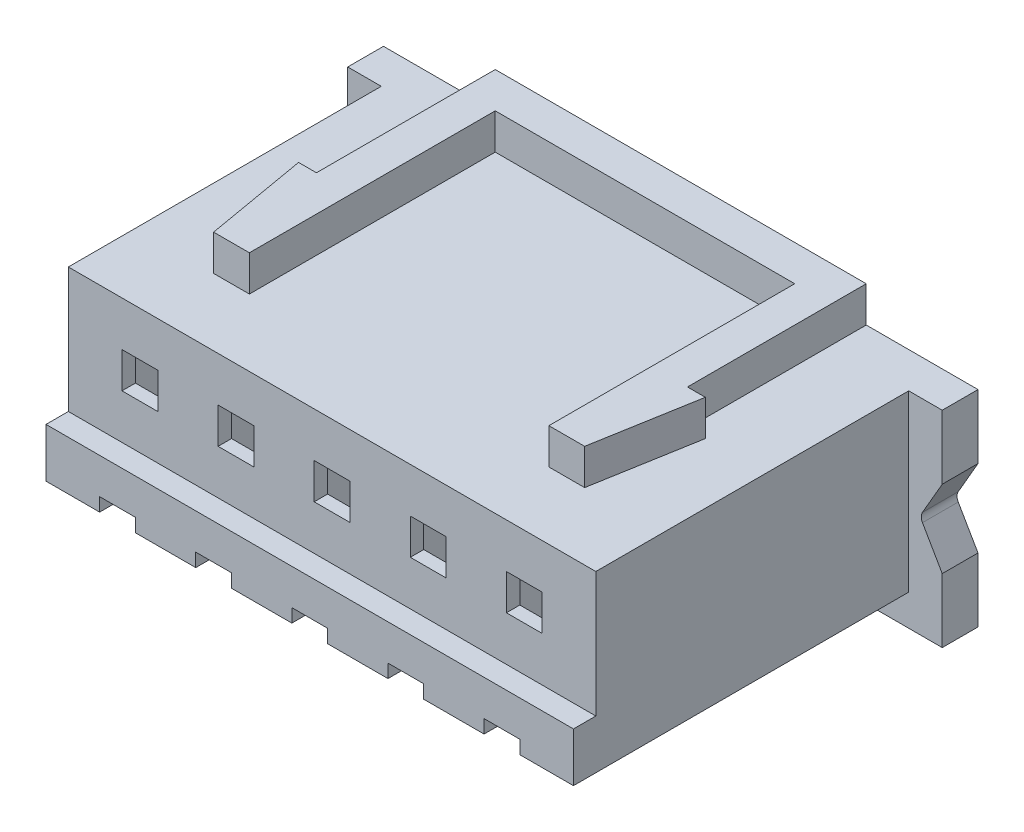
SolidWorks part; units mm, degrees
ref_plane "Front Plane" through (0, 0, 0) normal (0, 0, 1) x (1, 0, 0)
ref_plane "Top Plane" through (0, 0, 0) normal (0, 1, 0) x (1, 0, 0)
ref_plane "Right Plane" through (0, 0, 0) normal (1, 0, 0) x (0, 0, -1)
sketch "Sketch1" plane through (0, 0, 0) normal (0, 0, 1) x (1, 0, 0)
  line L1 (-5.9, -2.15) -> (5.9, -2.15)
  line L2 (-5.9, -2.15) -> (-5.9, 2.15)
  line L3 (-5.9, 2.15) -> (5.9, 2.15)
  line L4 (5.9, -2.15) -> (5.9, 2.15)
  line L5 (-5.9, -2.15) -> (5.9, 2.15) construction
  line L6 (-5.9, 2.15) -> (5.9, -2.15) construction
  point P0 (0, 0)
  dimension "D1" = 4.3
  dimension "D2" = 11.8
extrude "Boss-Extrude1" add sketch "Sketch1" along normal blind 7
sketch "Sketch2" plane through (0, 0, 0) normal (0, 0, -1) x (-1, 0, 0)
  line L0 (0, 0) -> (0, 2.15) construction
  line L1 (-6.65, 2.15) -> (6.65, 2.15)
  line L2 (-6.65, 2.15) -> (-6.65, -2.45)
  line L3 (-6.65, -2.45) -> (6.65, -2.45)
  line L4 (6.65, 2.15) -> (6.65, -2.45)
  dimension "D1" = 13.3
  dimension "D2" = 4.6
extrude "Boss-Extrude2" add sketch "Sketch2" along normal blind 0.8
sketch "Sketch3" plane through (0, 0, 0) normal (0, 0, 1) x (1, 0, 0)
  line L1 (6.65, 2.15) -> (6.65, -2.45) construction
  line L2 (6.15, -0.15) -> (6.65, -1.016)
  line L3 (6.15, -0.15) -> (6.65, 0.716)
  line L4 (6.65, -0.15) -> (6.15, -0.15) construction
  line L5 (6.65, 0.716) -> (6.65, -1.016)
  dimension "D1" = 60
  dimension "D2" = 0.5
  dimension "D3" = 60
extrude "Cut-Extrude1" cut sketch "Sketch3" against normal blind 1
fillet "Fillet1" radius 0.2 1 edges at (6.15, -0.15, -0.4)
sketch "Sketch4" plane through (0, 0, 7) normal (0, 0, 1) x (1, 0, 0)
  line L0 (-5.9, 2.15) -> (-5.9, -2.15) construction
  line L1 (-5.9, -0.65) -> (5.9, -0.65)
  line L2 (-5.9, -0.65) -> (-5.9, -2.15)
  line L3 (-5.9, -2.15) -> (5.9, -2.15)
  line L4 (5.9, -0.65) -> (5.9, -2.15)
  dimension "D1" = 1.5
extrude "Boss-Extrude3" add sketch "Sketch4" along normal blind 0.5
sketch "Sketch5" plane through (0, 0, 7.5) normal (0, 0, 1) x (1, 0, 0)
  line L0 (-5.9, -2.15) -> (5.9, -2.15) construction
  line L1 (-4.7, -1.45) -> (-3.9, -1.45)
  line L2 (-4.7, -1.45) -> (-4.7, -2.15)
  line L3 (-4.7, -2.15) -> (-3.9, -2.15)
  line L4 (-3.9, -1.45) -> (-3.9, -2.15)
  line L5 (-5.9, -0.65) -> (-5.9, -2.15) construction
  line L14 (3.9, -1.45) -> (4.7, -1.45)
  line L15 (4.7, -1.45) -> (4.7, -2.15)
  line L16 (3.9, -1.45) -> (3.9, -2.15)
  line L17 (3.9, -2.15) -> (4.7, -2.15)
  line L18 (5.9, -2.15) -> (5.9, -0.65) construction
  line L20 (1.75, -2.15) -> (2.55, -2.15)
  line L21 (1.75, -1.45) -> (1.75, -2.15)
  line L22 (1.75, -1.45) -> (2.55, -1.45)
  line L23 (2.55, -1.45) -> (2.55, -2.15)
  line L24 (-0.4, -2.15) -> (0.4, -2.15)
  line L25 (-0.4, -1.45) -> (-0.4, -2.15)
  line L26 (-0.4, -1.45) -> (0.4, -1.45)
  line L27 (0.4, -1.45) -> (0.4, -2.15)
  line L28 (-2.55, -2.15) -> (-1.75, -2.15)
  line L29 (-2.55, -1.45) -> (-2.55, -2.15)
  line L30 (-2.55, -1.45) -> (-1.75, -1.45)
  line L31 (-1.75, -1.45) -> (-1.75, -2.15)
  line L32 (-4.7, -2.15) -> (-3.9, -2.15)
  line L33 (-4.7, -1.45) -> (-4.7, -2.15)
  line L34 (-4.7, -1.45) -> (-3.9, -1.45)
  line L35 (-3.9, -1.45) -> (-3.9, -2.15)
  line L36 (-5.9, 2.15) -> (-5.9, -2.15) construction
  line L37 (1.0333, -1.45) -> (1.0333, -2.15) [skipped]
  line L38 (1.0333, -2.15) -> (1.8333, -2.15) [skipped]
  line L39 (1.8333, -1.45) -> (1.8333, -2.15) [skipped]
  line L40 (1.0333, -1.45) -> (1.8333, -1.45) [skipped]
  line L41 (-1.0333, -1.45) -> (-1.0333, -2.15) [skipped]
  line L42 (-1.8333, -2.15) -> (-1.0333, -2.15) [skipped]
  line L43 (-1.8333, -1.45) -> (-1.0333, -1.45) [skipped]
  line L44 (-1.8333, -1.45) -> (-1.8333, -2.15) [skipped]
  line M18 (-5.9, -2.15) -> (5.9, -2.15)
  dimension "D1" = 0.8
  dimension "D2" = 1.2
  dimension "D3" = 0.7
  dimension "D5" = 1.2
  dimension "D8" = 1.2
  dimension "D4" = 4
  dimension "D7" = 5
extrude "Cut-Extrude2" cut sketch "Sketch5" against normal blind 3.2 contours L14 L16 L15 M18 | L23 L22 L21 M18 | L27 L26 L25 M18 | L31 L30 L29 M18 | L4 L1 L2 M18
sketch "Sketch6" plane through (0, 0, 7) normal (0, 0, 1) x (1, 0, 0)
  line L0 (-5.9, 2.15) -> (-5.9, -0.65) construction
  line L1 (-4.7, 1.15) -> (-3.9, 1.15)
  line L2 (-4.7, 1.15) -> (-4.7, 0.35)
  line L3 (-4.7, 0.35) -> (-3.9, 0.35)
  line L4 (-3.9, 1.15) -> (-3.9, 0.35)
  line L5 (-1.75, 1.15) -> (-1.75, 0.35)
  line L6 (-2.55, 0.35) -> (-1.75, 0.35)
  line L7 (-2.55, 1.15) -> (-2.55, 0.35)
  line L8 (-2.55, 1.15) -> (-1.75, 1.15)
  line L9 (0.4, 1.15) -> (0.4, 0.35)
  line L10 (-0.4, 0.35) -> (0.4, 0.35)
  line L11 (-0.4, 1.15) -> (-0.4, 0.35)
  line L12 (-0.4, 1.15) -> (0.4, 1.15)
  line L13 (2.55, 1.15) -> (2.55, 0.35)
  line L14 (1.75, 0.35) -> (2.55, 0.35)
  line L15 (1.75, 1.15) -> (1.75, 0.35)
  line L16 (1.75, 1.15) -> (2.55, 1.15)
  line L18 (5.9, 2.15) -> (-5.9, 2.15) construction
  line L19 (4.7, 1.15) -> (4.7, 0.35)
  line L20 (3.9, 0.35) -> (4.7, 0.35)
  line L21 (3.9, 1.15) -> (3.9, 0.35)
  line L22 (3.9, 1.15) -> (4.7, 1.15)
  line L23 (5.9, -0.65) -> (5.9, 2.15) construction
  dimension "D1" = 0.8
  dimension "D2" = 0.8
  dimension "D3" = 1.2
  dimension "D5" = 1.2
  dimension "D6" = 1
  dimension "D4" = 5
extrude "Cut-Extrude3" cut sketch "Sketch6" against normal blind 10
sketch "Sketch7" plane through (0, 2.15, 0) normal (0, 1, 0) x (1, 0, 0)
  line L0 (-4.15, -5.5) -> (-4.55, -3.2)
  line L1 (-4.55, -3.2) -> (-4.15, -3.2)
  line L2 (-4.15, -3.2) -> (-4.15, 0.8)
  line L3 (-6.65, 0.8) -> (6.65, 0.8) construction
  line L4 (-4.15, 0.8) -> (4.15, 0.8)
  line L5 (4.15, 0.8) -> (4.15, -3.2)
  line L6 (4.15, -3.2) -> (4.55, -3.2)
  line L7 (4.55, -3.2) -> (4.15, -5.5)
  line L8 (4.15, -5.5) -> (3.35, -5.5)
  line L9 (3.35, -5.5) -> (3.35, 0)
  line L10 (3.35, 0) -> (-3.35, 0)
  line L11 (-3.35, 0) -> (-3.35, -5.5)
  line L12 (-3.35, -5.5) -> (-4.15, -5.5)
  line L13 (0, 0.8) -> (0, 0) construction
  dimension "D1" = 0.8
  dimension "D2" = 0.8
  dimension "D3" = 0.8
  dimension "D4" = 0.8
  dimension "D5" = 1.2
  dimension "D6" = 4
  dimension "D7" = 2.3
  dimension "D8" = 4
  dimension "D9" = 1.2
  dimension "D10" = 0.8
  dimension "D11" = 8.3
extrude "Boss-Extrude4" add sketch "Sketch7" along normal blind 0.8
sketch "Sketch8" plane through (0, 0, -0.8) normal (0, 0, -1) x (-1, 0, 0)
  line L1 (5.3, 1.75) -> (3.3, 1.75)
  line L2 (5.3, 1.75) -> (5.3, -1.05)
  line L3 (4.7, -1.05) -> (4.7, -1.45)
  line L4 (3.3, 1.75) -> (3.3, -1.05)
  line L5 (5.3, -1.05) -> (4.7, -1.05)
  line L6 (4.7, -1.45) -> (3.9, -1.45)
  line L7 (3.9, -1.45) -> (3.9, -1.05)
  line L8 (3.9, -1.05) -> (3.3, -1.05)
  line L11 (3.15, -1.05) -> (2.55, -1.05)
  line L12 (2.55, -1.05) -> (2.55, -1.45)
  line L13 (2.55, -1.45) -> (1.75, -1.45)
  line L14 (1.75, -1.05) -> (1.15, -1.05)
  line L15 (1.75, -1.45) -> (1.75, -1.05)
  line L16 (1.15, 1.75) -> (1.15, -1.05)
  line L17 (3.15, 1.75) -> (1.15, 1.75)
  line L18 (3.15, 1.75) -> (3.15, -1.05)
  line L19 (1, -1.05) -> (0.4, -1.05)
  line L20 (0.4, -1.05) -> (0.4, -1.45)
  line L21 (0.4, -1.45) -> (-0.4, -1.45)
  line L22 (-0.4, -1.05) -> (-1, -1.05)
  line L23 (-0.4, -1.45) -> (-0.4, -1.05)
  line L24 (-1, 1.75) -> (-1, -1.05)
  line L25 (1, 1.75) -> (-1, 1.75)
  line L26 (1, 1.75) -> (1, -1.05)
  line L27 (-1.15, -1.05) -> (-1.75, -1.05)
  line L28 (-1.75, -1.05) -> (-1.75, -1.45)
  line L29 (-1.75, -1.45) -> (-2.55, -1.45)
  line L30 (-2.55, -1.05) -> (-3.15, -1.05)
  line L31 (-2.55, -1.45) -> (-2.55, -1.05)
  line L32 (-3.15, 1.75) -> (-3.15, -1.05)
  line L33 (-1.15, 1.75) -> (-3.15, 1.75)
  line L34 (-1.15, 1.75) -> (-1.15, -1.05)
  line L37 (-3.3, -1.05) -> (-3.9, -1.05)
  line L38 (-3.9, -1.05) -> (-3.9, -1.45)
  line L39 (-3.9, -1.45) -> (-4.7, -1.45)
  line L40 (-4.7, -1.05) -> (-5.3, -1.05)
  line L41 (-4.7, -1.45) -> (-4.7, -1.05)
  line L42 (-5.3, 1.75) -> (-5.3, -1.05)
  line L43 (-3.3, 1.75) -> (-5.3, 1.75)
  line L44 (-3.3, 1.75) -> (-3.3, -1.05)
  line L45 (2.55, -1.45) -> (2.55, -2.15) construction
  dimension "D1" = 2.8
  dimension "D2" = 2
  dimension "D3" = 5
  dimension "D5" = 0.6
  dimension "D6" = 0.6
extrude "Cut-Extrude4" cut sketch "Sketch8" against normal blind 7.5
sketch "Sketch9" plane through (0, -2.15, 0) normal (0, -1, 0) x (1, 0, 0)
  line L22 (3.9, 7.5) -> (2.55, 7.5)
  line L25 (3.9, 4.3) -> (3.9, 7.5)
  line L26 (3.9, 4.3) -> (3.9, 7.5)
  line L27 (-2.55, 7.5) -> (-3.9, 7.5)
  line L28 (-2.55, 7.5) -> (-3.9, 7.5)
  line L29 (-3.9, 7.5) -> (-3.9, 4.3)
  line L30 (-3.9, 7.5) -> (-3.9, 4.3)
  line L31 (-4.7, 4.3) -> (-4.7, 7.5)
  line L32 (-4.7, 4.3) -> (-4.7, 7.5)
  line L33 (-4.7, 7.5) -> (-5.9, 7.5)
  line L34 (-4.7, 7.5) -> (-5.9, 7.5)
  line L35 (-5.9, 7.5) -> (-5.9, 0)
  line L36 (-5.9, 0) -> (5.9, 0)
  line L37 (5.9, 0) -> (5.9, 7.5)
  line L38 (5.9, 7.5) -> (4.7, 7.5)
  line L39 (5.9, 7.5) -> (4.7, 7.5)
  line L40 (4.7, 7.5) -> (4.7, 4.3)
  line L41 (4.7, 7.5) -> (4.7, 4.3)
  line L42 (3.9, 7.5) -> (2.55, 7.5)
  line L43 (-3.9, 4.3) -> (-4.7, 4.3)
  line L44 (-3.9, 4.3) -> (-4.7, 4.3)
  line L45 (4.7, 4.3) -> (3.9, 4.3)
  line L46 (4.7, 4.3) -> (3.9, 4.3)
  line L47 (2.55, 7.5) -> (2.55, 4.3)
  line L48 (2.55, 7.5) -> (2.55, 4.3)
  line L49 (2.55, 4.3) -> (1.75, 4.3)
  line L50 (2.55, 4.3) -> (1.75, 4.3)
  line L51 (1.75, 4.3) -> (1.75, 7.5)
  line L52 (1.75, 4.3) -> (1.75, 7.5)
  line L53 (1.75, 7.5) -> (0.4, 7.5)
  line L54 (1.75, 7.5) -> (0.4, 7.5)
  line L55 (-5.9, 7.5) -> (-5.9, 0)
  line L56 (-5.9, 0) -> (5.9, 0)
  line L57 (5.9, 0) -> (5.9, 7.5)
  line L58 (0.4, 7.5) -> (0.4, 4.3)
  line L59 (0.4, 7.5) -> (0.4, 4.3)
  line L60 (0.4, 4.3) -> (-0.4, 4.3)
  line L61 (0.4, 4.3) -> (-0.4, 4.3)
  line L62 (-0.4, 4.3) -> (-0.4, 7.5)
  line L63 (-0.4, 4.3) -> (-0.4, 7.5)
  line L64 (-0.4, 7.5) -> (-1.75, 7.5)
  line L65 (-0.4, 7.5) -> (-1.75, 7.5)
  line L66 (-1.75, 7.5) -> (-1.75, 4.3)
  line L67 (-1.75, 7.5) -> (-1.75, 4.3)
  line L68 (-1.75, 4.3) -> (-2.55, 4.3)
  line L69 (-1.75, 4.3) -> (-2.55, 4.3)
  line L70 (-2.55, 4.3) -> (-2.55, 7.5)
  line L71 (-2.55, 4.3) -> (-2.55, 7.5)
  dimension "D1" = 0
extrude "Cut-Extrude5" cut sketch "Sketch9" against normal blind 0.4
sketch "Sketch10" plane through (0, 0, -0.8) normal (0, 0, -1) x (-1, 0, 0)
  line L0 (-6.1451, -2.1537) -> (5.8088, -2.1537) construction
  text T0 "         1         2         3         4         5" font "Century Gothic" height 0.5
extrude "Boss-Extrude5" add sketch "Sketch10" along normal blind 0.1
